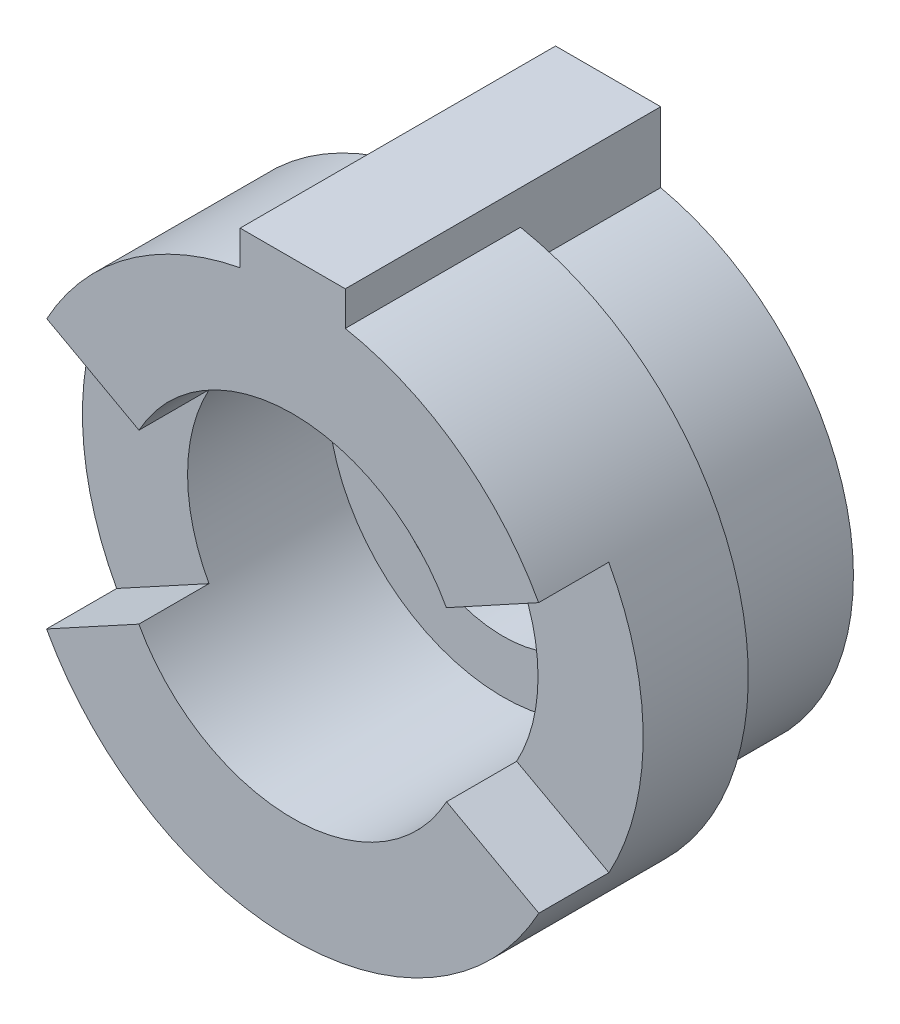
SolidWorks part; units mm, degrees
ref_plane "Front Plane" through (0, 0, 0) normal (0, 0, 1) x (1, 0, 0)
ref_plane "Top Plane" through (0, 0, 0) normal (0, 1, 0) x (1, 0, 0)
ref_plane "Right Plane" through (0, 0, 0) normal (1, 0, 0) x (0, 0, -1)
sketch "Sketch1" plane through (0, 0, 0) normal (0, 0, 1) x (1, 0, 0)
  circle A0 centre (0, 0) radius 8
  circle A1 centre (0, 0) radius 3.5
  dimension "D1" = 7
  dimension "D2" = 16
extrude "Boss-Extrude1" add sketch "Sketch1" along normal blind 3
sketch "Sketch2" plane through (0, 0, 3) normal (0, 0, 1) x (1, 0, 0)
  circle A0 centre (0, 0) radius 8
  circle A1 centre (0, 0) radius 5
  dimension "D1" = 16
  dimension "D2" = 10
extrude "Boss-Extrude2" add sketch "Sketch2" along normal blind 6
sketch "Sketch4" plane through (0, 0, 0) normal (0, 1, 0) x (1, 0, 0)
  line L0 (-8.56, -9) -> (-8.56, -7)
  line L1 (-16.56, -9) -> (-8.56, -9)
  line L2 (8.56, -9) -> (8.56, -7)
  line L3 (8.56, -9) -> (16.56, -9)
  line L4 (-16.56, -9) -> (-16.56, -7)
  line L5 (-16.56, -7) -> (-8.56, -7)
  line L6 (16.56, -9) -> (16.56, -7)
  line L7 (16.56, -7) -> (8.56, -7)
  dimension "D1" = 7
  dimension "D2" = 8.56
  dimension "D3" = 2
  dimension "D4" = 8.56
  dimension "D5" = 8
  dimension "D6" = 8
  dimension "D7" = 2
  dimension "D8" = 7
wrap "Wrap3" sketch "Sketch4" wrap type deboss source sketch "Sketch4" thickness 4 face at (8, 0, 0) parameters "D1"=4
sketch "Sketch5" plane through (0, 0, 0) normal (0, 0, -1) x (-1, 0, 0)
  line L0 (-1.5, 6.8374) -> (-1.5, 7.8581)
  line L2 (1.5, 7.8581) -> (1.5, 6.8374)
  arc A0 (-1.5, 7.8581) -> (1.5, 7.8581) centre (0, 0) ccw
  arc A1 (-1.5, 6.8374) -> (1.5, 6.8374) centre (0, 0) ccw
  circle A2 centre (0, 0) radius 8 construction
  dimension "D1" = 8
  dimension "D3" = 7
  dimension "D2" = 1.5
extrude "Cut-Extrude1" cut sketch "Sketch5" against normal blind 4
sketch "Sketch6" plane through (0, 0, 0) normal (0, 0, -1) x (-1, 0, 0)
  line L0 (-1.5, 7.8581) -> (-1.5, 8.8374)
  line L1 (-1.5, 8.8374) -> (1.5, 8.8374)
  line L2 (1.5, 8.8374) -> (1.5, 7.8581)
  line L3 (-1.5, 6.8374) -> (-1.5, 7.8581) construction
  arc A0 (1.5, 7.8581) -> (-1.5, 7.8581) centre (0, 0) ccw
  dimension "D1" = 8
  dimension "D2" = 1.5
  dimension "D3" = 1.0207
  dimension "D4" = 2
extrude "Boss-Extrude3" add sketch "Sketch6" against normal blind 9
